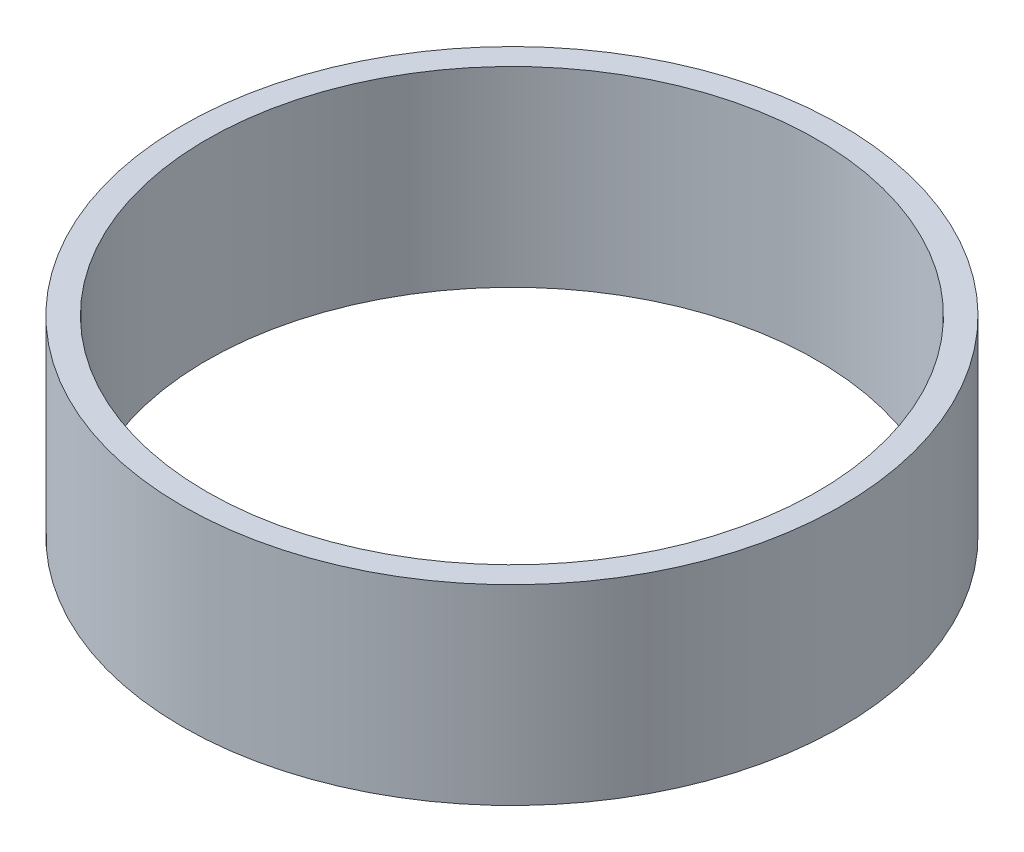
SolidWorks part; units mm, degrees
ref_plane "Front Plane" through (0, 0, 0) normal (0, 0, 1) x (1, 0, 0)
ref_plane "Top Plane" through (0, 0, 0) normal (0, 1, 0) x (1, 0, 0)
ref_plane "Right Plane" through (0, 0, 0) normal (1, 0, 0) x (0, 0, -1)
sketch "Sketch1" plane through (0, 0, 0) normal (0, 1, 0) x (1, 0, 0)
  circle A0 centre (0, 0) radius 40.5
  circle A1 centre (0, 0) radius 37.5
  dimension "D1" = 75
  dimension "D2" = 3
extrude "Boss-Extrude1" add sketch "Sketch1" along normal blind 23.5
